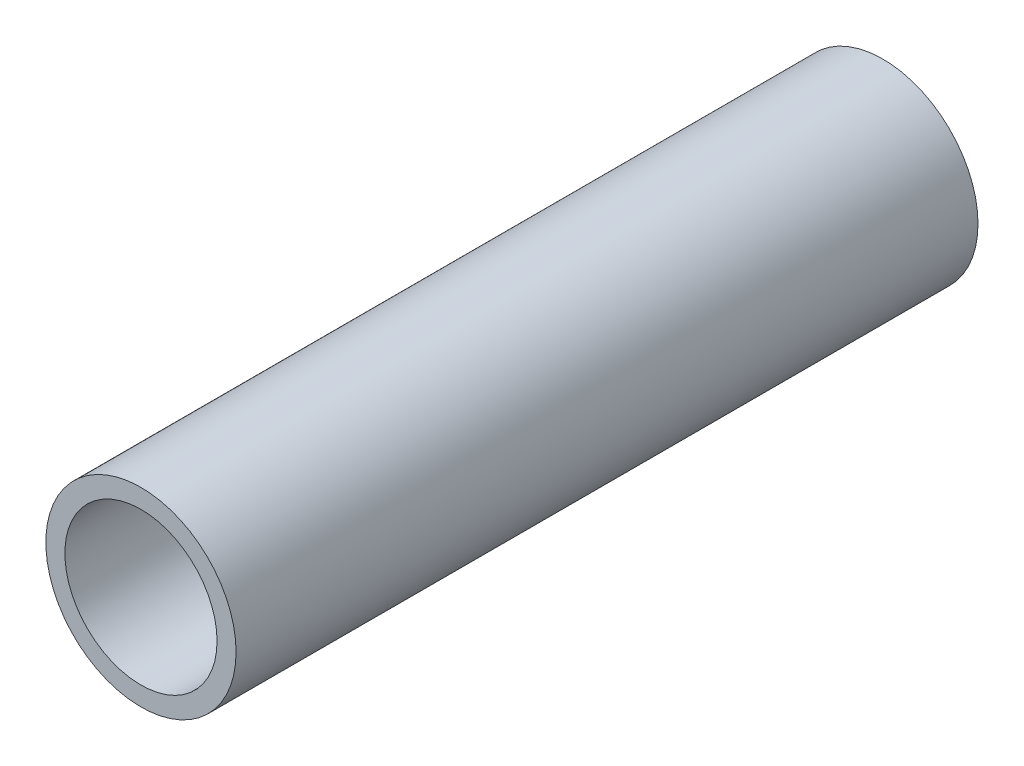
SolidWorks part; units mm, degrees
material "Alu 6060 (AGS)"
ref_plane "Face" through (0, 0, 0) normal (0, 0, 1) x (1, 0, 0)
ref_plane "Dessus" through (0, 0, 0) normal (0, 1, 0) x (1, 0, 0)
ref_plane "Droite" through (0, 0, 0) normal (1, 0, 0) x (0, 0, -1)
sketch "Esquisse1" plane through (0, 0, 0) normal (0, 0, 1) x (1, 0, 0)
  circle A0 centre (0, 0) radius 10
  circle A1 centre (0, 0) radius 8
  dimension "D1" = 20
  dimension "D2" = 16
extrude "Boss.-Extru.1" add sketch "Esquisse1" along normal mid plane 78
